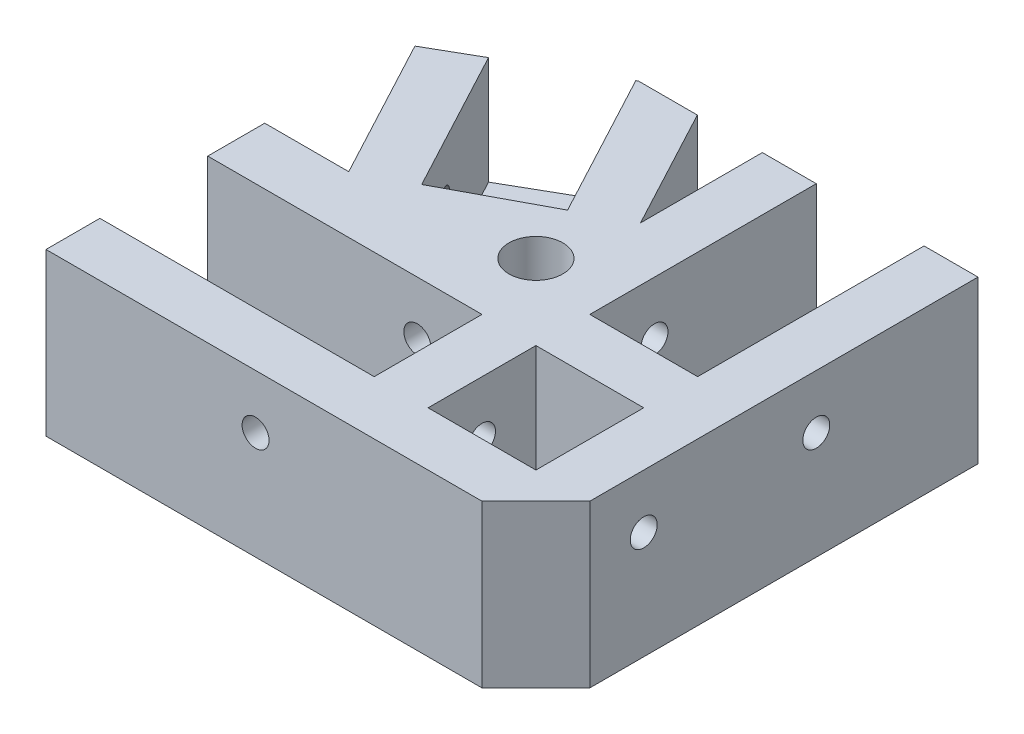
SolidWorks part; units mm, degrees
ref_plane "Alzado" through (0, 0, 0) normal (0, 0, 1) x (1, 0, 0)
ref_plane "Planta" through (0, 0, 0) normal (0, 1, 0) x (1, 0, 0)
ref_plane "Vista lateral" through (0, 0, 0) normal (1, 0, 0) x (0, 0, -1)
sketch "Croquis1" plane through (0, 0, 0) normal (0, 1, 0) x (1, 0, 0)
  line L0 (25.4, 78.74) -> (25.4, -12.7)
  line L1 (-12.7, 12.7) -> (12.7, 12.7) construction
  line L2 (-12.7, 12.7) -> (-12.7, -12.7) construction
  line L3 (-12.7, -12.7) -> (12.7, -12.7) construction
  line L4 (12.7, 12.7) -> (12.7, -12.7) construction
  line L5 (-12.7, 12.7) -> (12.7, -12.7) construction
  line L6 (-12.7, -12.7) -> (12.7, 12.7) construction
  line L7 (-12.7, 50.8) -> (12.7, 50.8) construction
  line L8 (-12.7, 50.8) -> (-12.7, 25.4) construction
  line L9 (-12.7, 25.4) -> (12.7, 25.4) construction
  line L10 (12.7, 50.8) -> (12.7, 25.4) construction
  line L11 (-12.7, 50.8) -> (12.7, 25.4) construction
  line L12 (-12.7, 25.4) -> (12.7, 50.8) construction
  line L13 (-69.9589, 25.654) -> (-25.654, 50.508) construction
  line L14 (-25.654, 50.508) -> (-38.081, 72.6604) construction
  line L15 (-38.081, 72.6604) -> (-82.3858, 47.8064) construction
  line L16 (-82.3858, 47.8064) -> (-69.9589, 25.654) construction
  line L17 (12.7, -25.4) -> (-90.0058, -25.4)
  line L18 (-50.8, 12.7) -> (-25.4, 12.7) construction
  line L19 (-50.8, 12.7) -> (-50.8, -12.7) construction
  line L20 (-50.8, -12.7) -> (-25.4, -12.7) construction
  line L21 (-25.4, 12.7) -> (-25.4, -12.7) construction
  line L22 (-50.8, 12.7) -> (-25.4, -12.7) construction
  line L23 (-50.8, -12.7) -> (-25.4, 12.7) construction
  line L24 (-98.4509, 21.1712) -> (-38.3204, 21.1712) construction
  line L25 (-38.3204, 21.1712) -> (-78.1604, 92.1901) construction
  line L26 (-90.0058, -25.4) -> (-90.0058, 58.42)
  line L27 (-90.0058, 58.42) -> (-54.5524, 78.74)
  line L28 (-54.5524, 78.74) -> (25.4, 78.74)
  line L29 (12.7, -25.4) -> (25.4, -12.7)
  point P0 (0, 0)
  point P6 (0, 38.1)
  point P15 (-38.1, 0)
  point P26 (-60.2334, 60.2334)
  point P28 (-47.8064, 38.081)
  dimension "D1" = 25.4
  dimension "D2" = 25.4
  dimension "D3" = 25.4
  dimension "D4" = 25.4
  dimension "D5" = 12.7
  dimension "D6" = 12.7
  dimension "D7" = 12.7
  dimension "D8" = 25.4
  dimension "D9" = 25.4
  dimension "D10" = 12.7
  dimension "D11" = 60.709
  dimension "D12" = 12.954
  dimension "D13" = 7.62
  dimension "D14" = 12.954
  dimension "D15" = 50.8
  dimension "D16" = 25.4
  dimension "D17" = 12.7
  dimension "D18" = 91.44
  dimension "D19" = 83.82
  dimension "D20" = 40.8638
  dimension "D21" = 17.9605
extrude "Saliente-Extruir1" add sketch "Croquis1" along normal blind 38.1
sketch "Croquis2" plane through (0, 38.1, 0) normal (0, 1, 0) x (1, 0, 0)
  line L1 (-12.7, 12.7) -> (12.7, 12.7)
  line L2 (-12.7, 12.7) -> (-12.7, -12.7)
  line L3 (-12.7, -12.7) -> (12.7, -12.7)
  line L4 (12.7, 12.7) -> (12.7, -12.7)
  line L5 (-12.7, 12.7) -> (12.7, -12.7) construction
  line L6 (-12.7, -12.7) -> (12.7, 12.7) construction
  point P0 (0, 0)
  dimension "D1" = 25.4
  dimension "D2" = 25.4
extrude "Cortar-Extruir1" cut sketch "Croquis2" against normal blind 25.4
sketch "Croquis3" plane through (0, 38.1, 0) normal (0, 1, 0) x (1, 0, 0)
  line L0 (-12.7, 12.7) -> (-12.7, -12.7) construction
  line L1 (-90.0058, 12.7) -> (-25.4, 12.7)
  line L2 (-90.0058, 12.7) -> (-90.0058, -12.7)
  line L3 (-90.0058, -12.7) -> (-25.4, -12.7)
  line L4 (-25.4, 12.7) -> (-25.4, -12.7)
  line L5 (-90.0058, 12.7) -> (-25.4, -12.7) construction
  line L6 (-90.0058, -12.7) -> (-25.4, 12.7) construction
  line L7 (-90.0058, 58.42) -> (-90.0058, -25.4) construction
  point P0 (-57.7029, 0)
  dimension "D2" = 25.4
  dimension "D3" = 12.7
extrude "Cortar-Extruir2" cut sketch "Croquis3" against normal blind 25.4
sketch "Croquis4" plane through (0, 38.1, 0) normal (0, 1, 0) x (1, 0, 0)
  line L0 (25.4, -12.7) -> (25.4, 78.74) construction
  line L1 (-12.7, 78.74) -> (12.7, 78.74)
  line L2 (-12.7, 78.74) -> (-12.7, 25.4)
  line L3 (-12.7, 25.4) -> (12.7, 25.4)
  line L4 (12.7, 78.74) -> (12.7, 25.4)
  line L5 (-12.7, 78.74) -> (12.7, 25.4) construction
  line L6 (-12.7, 25.4) -> (12.7, 78.74) construction
  line L7 (12.7, 12.7) -> (-12.7, 12.7) construction
  line L8 (25.4, 78.74) -> (-54.5524, 78.74) construction
  point P0 (0, 52.07)
  dimension "D2" = 25.4
  dimension "D3" = 12.7
  dimension "D4" = 12.7
extrude "Cortar-Extruir3" cut sketch "Croquis4" against normal blind 25.4
sketch "Croquis5" plane through (0, 38.1, 0) normal (0, 1, 0) x (1, 0, 0)
  line L2 (-47.8064, 38.081) -> (-90.0058, 38.081) construction
  line L15 (-47.8064, 38.081) -> (25.4, 38.081) construction
  line L17 (25.4, -12.7) -> (25.4, 78.74) construction
  line L20 (-47.8064, 38.081) -> (-47.8064, -25.4) construction
  line L21 (-90.0058, -25.4) -> (12.7, -25.4) construction
  line L22 (-90.0058, 58.42) -> (-90.0058, 12.7) construction
  line L23 (-47.8064, 38.081) -> (-66.0006, 72.1785) construction
  line L24 (-54.5524, 78.74) -> (-90.0058, 58.42) construction
  line L25 (-59.0111, 32.1022) -> (-36.6018, 44.0597)
  line L26 (-36.6018, 44.0597) -> (-54.9771, 78.4966)
  line L27 (-59.0111, 32.1022) -> (-77.0242, 65.8604)
  line L28 (-77.0242, 65.8604) -> (-54.9771, 78.4966)
  point P11 (-47.8064, 38.081)
  dimension "D1" = 63.481
  dimension "D2" = 42.1994
  dimension "D3" = 61.916
  dimension "D4" = 25.4
extrude "Cortar-Extruir4" cut sketch "Croquis5" against normal blind 25.4
sketch "Croquis6" plane through (0, 38.1, 0) normal (0, 1, 0) x (1, 0, 0)
  line L8 (-70.2158, 26.1235) -> (-25.3971, 50.0385) construction
  line L16 (-59.0111, 32.1022) -> (-36.6018, 44.0597) construction
  line L17 (-25.3971, 50.0385) -> (-40.712, 78.74)
  line L18 (-70.2158, 26.1235) -> (-88.0478, 59.5422)
  line L19 (-12.7, 78.74) -> (-54.5524, 78.74) construction
  line L20 (-77.0242, 65.8604) -> (-90.0058, 58.42) construction
  line L21 (-25.3971, 50.0385) -> (-25.3971, 78.74)
  line L22 (-25.3971, 78.74) -> (-40.712, 78.74)
  line L23 (-70.2158, 26.1235) -> (-90.0058, 26.1235)
  line L24 (-90.0058, 58.42) -> (-90.0058, 12.7) construction
  line L25 (-90.0058, 26.1235) -> (-90.0058, 58.42)
  line L26 (-90.0058, 58.42) -> (-88.0478, 59.5422)
  point P4 (-47.8064, 38.081)
  point P5 (-47.8064, 38.081)
  dimension "D1" = 50.8
extrude "Cortar-Extruir5" cut sketch "Croquis6" against normal blind 25.4
sketch "Croquis7" plane through (0, 0, 25.4) normal (0, 0, 1) x (1, 0, 0)
  line L0 (12.7, 38.1) -> (12.7, 0) construction
  line L1 (-90.0058, 38.1) -> (12.7, 38.1) construction
  circle A0 centre (-40.64, 25.4) radius 3.175
  dimension "D1" = 6.35
  dimension "D2" = 53.34
  dimension "D3" = 12.7
extrude "Cortar-Extruir6" cut sketch "Croquis7" against normal blind 50.8
sketch "Croquis8" plane through (25.4, 0, 0) normal (1, 0, 0) x (0, 0, -1)
  line L0 (-12.7, 38.1) -> (-12.7, 0) construction
  line L1 (-12.7, 38.1) -> (78.74, 38.1) construction
  circle A0 centre (40.64, 25.4) radius 3.175
  dimension "D1" = 6.35
  dimension "D2" = 53.34
  dimension "D3" = 12.7
extrude "Cortar-Extruir7" cut sketch "Croquis8" against normal blind 50.8
sketch "Croquis10" plane through (25.4, 0, 0) normal (1, 0, 0) x (0, 0, -1)
  line L0 (-12.7, 38.1) -> (78.74, 38.1) construction
  line L1 (-12.7, 38.1) -> (-12.7, 0) construction
  circle A0 centre (0, 25.4) radius 3.175
  dimension "D1" = 6.35
  dimension "D2" = 12.7
  dimension "D3" = 12.7
extrude "Cortar-Extruir9" cut sketch "Croquis10" against normal blind 43.18
ref_plane "Plano3" through (-115.4058, 0, 0) normal (-1, 0, 0) x (0, 0, 1)
sketch "Croquis11" plane through (-43.8044, 0, 23.3737) normal (-0.8823, 0, 0.4708) x (0.4708, 0, 0.8823)
  line L0 (-56.1029, 38.1) -> (-93.9816, 38.1) construction
  line L1 (-56.1029, 12.7) -> (-56.1029, 38.1) construction
  circle A0 centre (-69.0569, 25.4) radius 3.175
  dimension "D1" = 6.35
  dimension "D2" = 12.7
  dimension "D3" = 12.954
extrude "Cortar-Extruir10" cut sketch "Croquis11" against normal blind 50.8
sketch "Sketch1" plane through (0, 38.1, 0) normal (0, 1, 0) x (1, 0, 0)
  line L0 (25.4, -12.7) -> (25.4, 78.74) construction
  line L1 (-90.0058, -25.4) -> (12.7, -25.4) construction
  circle A0 centre (-30.48, 30.48) radius 6.35
  dimension "D1" = 12.7
  dimension "D2" = 55.88
  dimension "D3" = 55.88
extrude "Cut-Extrude1" cut sketch "Sketch1" against normal through all contours A0
ref_plane "Plane1" through (-21.395, 0, 11.4162) normal (-0.8823, 0, 0.4708) x (0.4708, 0, 0.8823)
